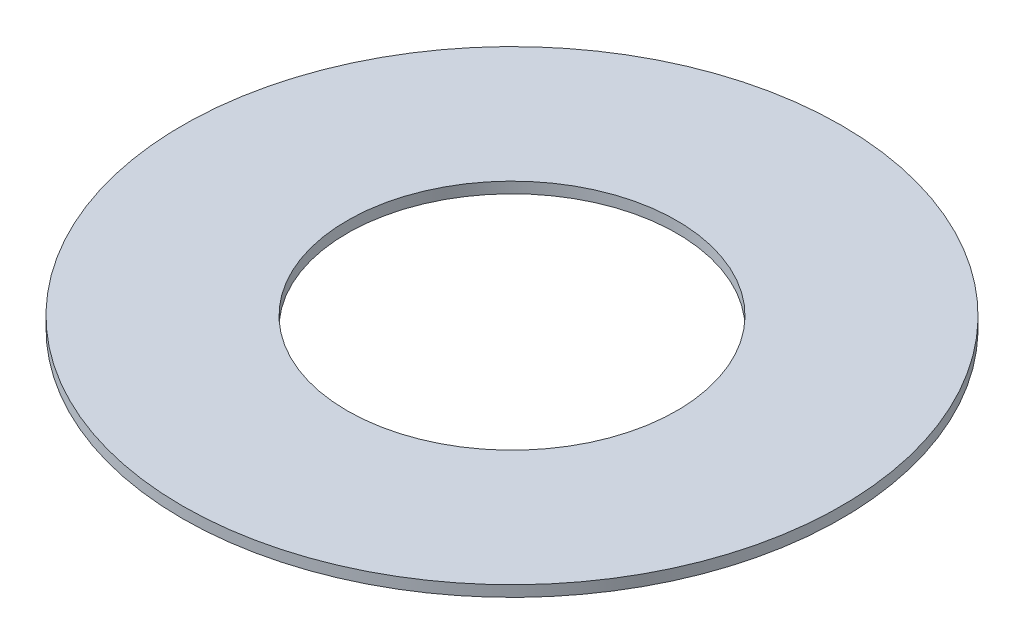
SolidWorks part; units mm, degrees
ref_plane "Front Plane" through (0, 0, 0) normal (0, 0, 1) x (1, 0, 0)
ref_plane "Top Plane" through (0, 0, 0) normal (0, 1, 0) x (1, 0, 0)
ref_plane "Right Plane" through (0, 0, 0) normal (1, 0, 0) x (0, 0, -1)
sketch "Sketch1" plane through (0, 0, 0) normal (0, 1, 0) x (1, 0, 0)
  circle A0 centre (0, 0) radius 6
  dimension "OD" = 12
extrude "Boss-Extrude1" add sketch "Sketch1" along normal blind 0.2
sketch "Sketch5" plane through (0, 0.2, 0) normal (0, 1, 0) x (-1, 0, 0)
  circle A0 centre (0, 0) radius 3
  dimension "ID" = 6
extrude "Cut-Extrude1" cut sketch "Sketch5" against normal through all
